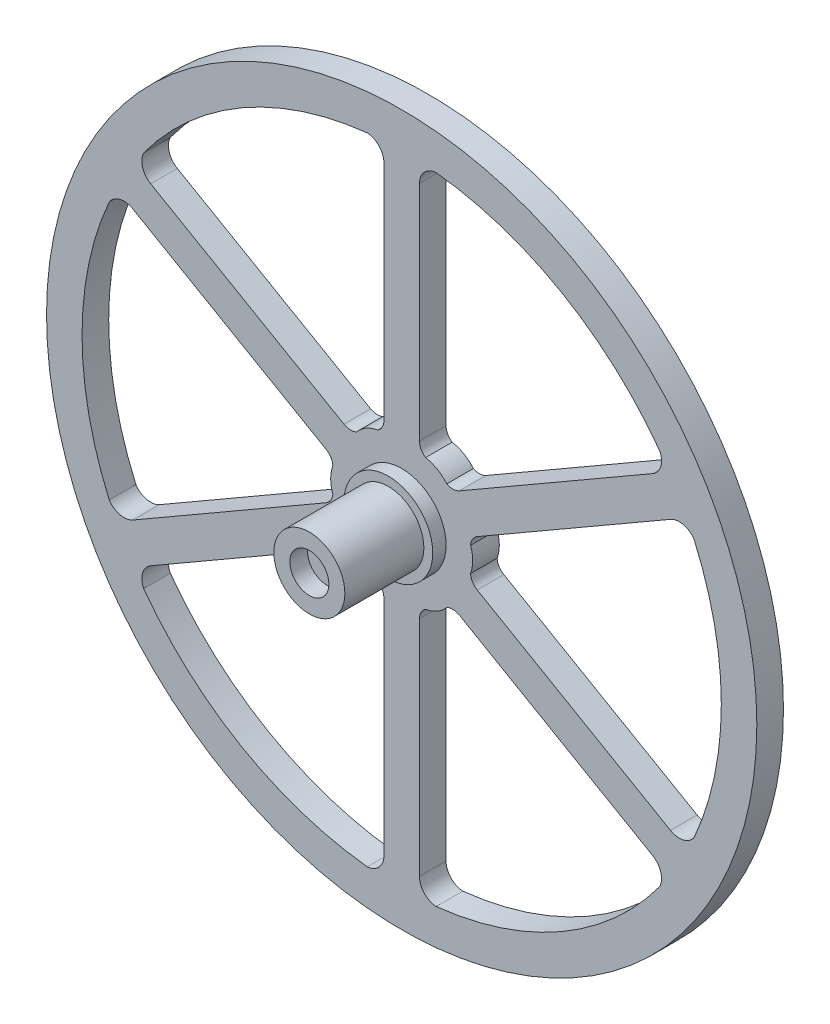
SolidWorks part; units mm, degrees
ref_plane "Front Plane" through (0, 0, 0) normal (0, 0, 1) x (1, 0, 0)
ref_plane "Top Plane" through (0, 0, 0) normal (0, 1, 0) x (1, 0, 0)
ref_plane "Right Plane" through (0, 0, 0) normal (1, 0, 0) x (0, 0, -1)
sketch "Sketch1" plane through (0, 0, 0) normal (0, 0, 1) x (1, 0, 0)
  circle A0 centre (0, 0) radius 4
  dimension "D1" = 8
extrude "Boss-Extrude1" add sketch "Sketch1" along normal blind 8.9
sketch "Sketch2" plane through (0, 0, 0) normal (0, 0, 1) x (1, 0, 0)
  circle A0 centre (0, 0) radius 5
  circle A1 centre (0, 0) radius 4 construction
  dimension "D1" = 1
extrude "Boss-Extrude2" add sketch "Sketch2" against normal blind 1.5
sketch "Sketch3" plane through (0, 0, 0) normal (0, 0, 1) x (1, 0, 0)
  circle A0 centre (0, 0) radius 40
  dimension "D1" = 80
extrude "Boss-Extrude3" add sketch "Sketch3" against normal blind 3 from surface at -1.5 starting at face at (5, 0, -1.5)
sketch "Sketch5" plane through (0, 0, 0) normal (0, 0, 1) x (1, 0, 0)
  circle A0 centre (0, 0) radius 2.2
  dimension "D1" = 4.4
extrude "Cut-Extrude2" cut sketch "Sketch5" against normal blind 2 from surface at 8.9 starting at face at (4, 0, 8.9)
sketch "Sketch6" plane through (0, 0, 0) normal (0, 0, 1) x (1, 0, 0)
  line L0 (0, 0) -> (0, 40) construction
  line L1 (30.2668, -15.1651) -> (8.5033, -2.6)
  line L2 (-1, 1.7321) -> (33.641, 21.7321) construction
  line L3 (2, 0) -> (2, 40) construction
  line L4 (0, 0) -> (22.1652, 38.3913) construction
  line L5 (2, 33.7944) -> (2, 8.6641)
  line L6 (28.2668, 18.6293) -> (6.5033, 6.0641)
  line L7 (30.2668, 15.1651) -> (8.5033, 2.6)
  line L8 (2, -33.7944) -> (2, -8.6641)
  line L9 (28.2668, -18.6293) -> (6.5033, -6.0641)
  line L10 (-28.2668, -18.6293) -> (-6.5033, -6.0641)
  line L11 (-2, -33.7944) -> (-2, -8.6641)
  line L12 (-30.2668, 15.1651) -> (-8.5033, 2.6)
  line L13 (-30.2668, -15.1651) -> (-8.5033, -2.6)
  line L14 (-2, 33.7944) -> (-2, 8.6641)
  line L15 (-28.2668, 18.6293) -> (-6.5033, 6.0641)
  circle A0 centre (0, 0) radius 40 construction
  arc A1 (2, 7.4641) -> (5.4641, 5.4641) centre (2, 3.4641) cw construction
  arc A2 (2, 35.9444) -> (30.1288, 19.7043) centre (0, 0) cw construction
  arc A3 (2, 33.7944) -> (3.8771, 35.7906) centre (4, 33.7944) cw
  arc A4 (2, 8.6641) -> (2.6846, 7.4051) centre (3.5, 8.6641) ccw
  arc A5 (2.6846, 7.4051) -> (5.0707, 6.0275) centre (2, 3.4641) cw
  arc A6 (3.8771, 35.7906) -> (29.0571, 21.2529) centre (0, 0) cw
  arc A7 (28.2668, 18.6293) -> (29.0571, 21.2529) centre (27.2668, 20.3613) ccw
  arc A8 (6.5033, 6.0641) -> (5.0707, 6.0275) centre (5.7533, 7.3631) cw
  arc A9 (8.5033, -2.6) -> (7.7553, -1.3776) centre (9.2533, -1.301) cw
  arc A10 (7.7553, 1.3776) -> (7.7553, -1.3776) centre (4, 0) cw
  arc A11 (8.5033, 2.6) -> (7.7553, 1.3776) centre (9.2533, 1.301) ccw
  arc A12 (30.2668, 15.1651) -> (32.9341, 14.5377) centre (31.2668, 13.4331) cw
  arc A13 (32.9341, 14.5377) -> (32.9341, -14.5377) centre (0, 0) cw
  arc A14 (30.2668, -15.1651) -> (32.9341, -14.5377) centre (31.2668, -13.4331) ccw
  arc A15 (2, -8.6641) -> (2.6846, -7.4051) centre (3.5, -8.6641) cw
  arc A16 (5.0707, -6.0275) -> (2.6846, -7.4051) centre (2, -3.4641) cw
  arc A17 (6.5033, -6.0641) -> (5.0707, -6.0275) centre (5.7533, -7.3631) ccw
  arc A18 (28.2668, -18.6293) -> (29.0571, -21.2529) centre (27.2668, -20.3613) cw
  arc A19 (29.0571, -21.2529) -> (3.8771, -35.7906) centre (0, 0) cw
  arc A20 (2, -33.7944) -> (3.8771, -35.7906) centre (4, -33.7944) ccw
  arc A21 (-6.5033, -6.0641) -> (-5.0707, -6.0275) centre (-5.7533, -7.3631) cw
  arc A22 (-2.6846, -7.4051) -> (-5.0707, -6.0275) centre (-2, -3.4641) cw
  arc A23 (-2, -8.6641) -> (-2.6846, -7.4051) centre (-3.5, -8.6641) ccw
  arc A24 (-2, -33.7944) -> (-3.8771, -35.7906) centre (-4, -33.7944) cw
  arc A25 (-3.8771, -35.7906) -> (-29.0571, -21.2529) centre (0, 0) cw
  arc A26 (-28.2668, -18.6293) -> (-29.0571, -21.2529) centre (-27.2668, -20.3613) ccw
  arc A27 (-8.5033, 2.6) -> (-7.7553, 1.3776) centre (-9.2533, 1.301) cw
  arc A28 (-7.7553, -1.3776) -> (-7.7553, 1.3776) centre (-4, 0) cw
  arc A29 (-8.5033, -2.6) -> (-7.7553, -1.3776) centre (-9.2533, -1.301) ccw
  arc A30 (-30.2668, -15.1651) -> (-32.9341, -14.5377) centre (-31.2668, -13.4331) cw
  arc A31 (-32.9341, -14.5377) -> (-32.9341, 14.5377) centre (0, 0) cw
  arc A32 (-30.2668, 15.1651) -> (-32.9341, 14.5377) centre (-31.2668, 13.4331) ccw
  arc A33 (-2, 8.6641) -> (-2.6846, 7.4051) centre (-3.5, 8.6641) cw
  arc A34 (-5.0707, 6.0275) -> (-2.6846, 7.4051) centre (-2, 3.4641) cw
  arc A35 (-6.5033, 6.0641) -> (-5.0707, 6.0275) centre (-5.7533, 7.3631) ccw
  arc A36 (-28.2668, 18.6293) -> (-29.0571, 21.2529) centre (-27.2668, 20.3613) cw
  arc A37 (-29.0571, 21.2529) -> (-3.8771, 35.7906) centre (0, 0) cw
  arc A38 (-2, 33.7944) -> (-3.8771, 35.7906) centre (-4, 33.7944) ccw
  point P7 (4, 6.9282)
  point P11 (2, 3.4641)
  point P17 (4, 33.7944)
  point P18 (3.5, 8.6641)
  point P100 (0, 0)
  dimension "D4" = 4
  dimension "D5" = 4
  dimension "D3" = 6
  dimension "D6" = 30
  dimension "D7" = 2.15
  dimension "D8" = 2
  dimension "D9" = 1.5
  dimension "D10" = 1.2
  dimension "D2" = 2
extrude "Cut-Extrude3" cut sketch "Sketch6" against normal blind 10
